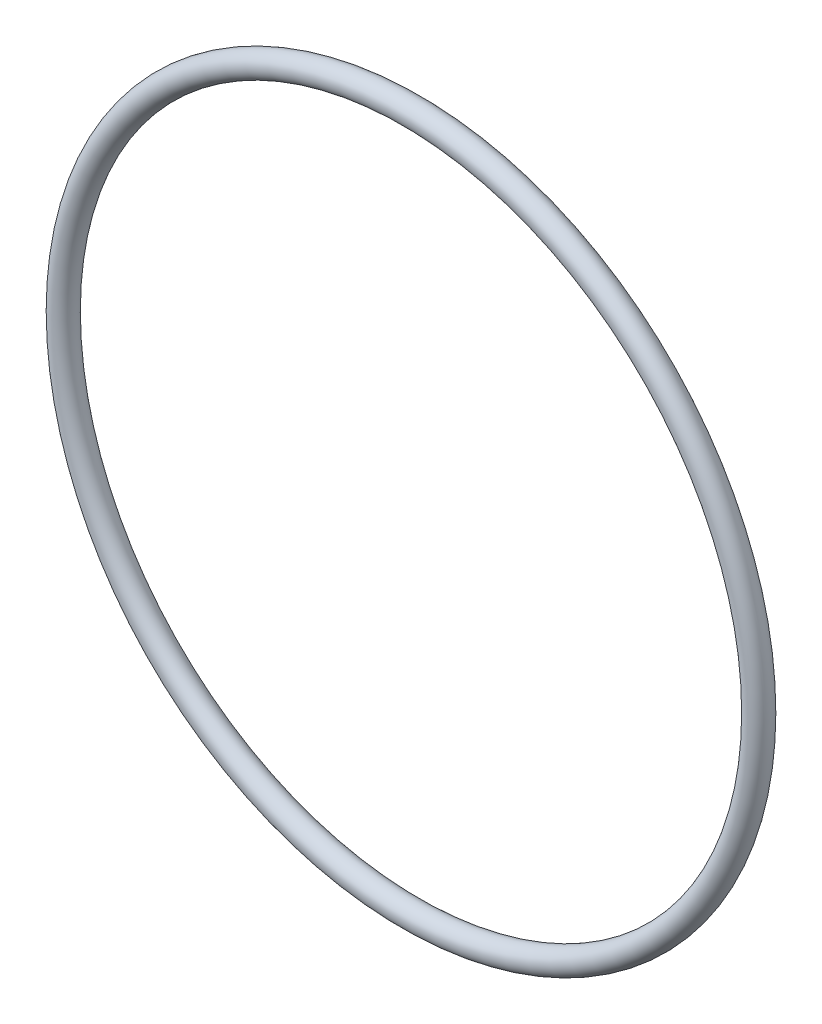
SolidWorks part; units mm, degrees
ref_plane "Front" through (0, 0, 0) normal (0, 0, 1) x (1, 0, 0)
ref_plane "Top" through (0, 0, 0) normal (0, 1, 0) x (1, 0, 0)
ref_plane "Right" through (0, 0, 0) normal (1, 0, 0) x (0, 0, -1)
sketch "Sketch1" plane through (0, 0, 0) normal (1, 0, 0) x (0, -1, 0)
  line L0 (0, -1.7653) -> (0, 1.7653) construction
  line L2 (-57.7939, 0) -> (57.7939, 0) construction
  line L3 (-49.0093, 0) -> (49.0093, 0) construction
  circle A0 centre (50.7746, 0) radius 1.7653
  point P9 (49.0093, 0)
  point P10 (52.5399, 0)
  point P13 (50.7746, 1.7653)
  point P14 (50.7746, -1.7653)
  dimension "Width" = 3.5306
  dimension "ID" = 98.0186
revolve "Revolve1" add sketch "Sketch1" angle 360 about L0
